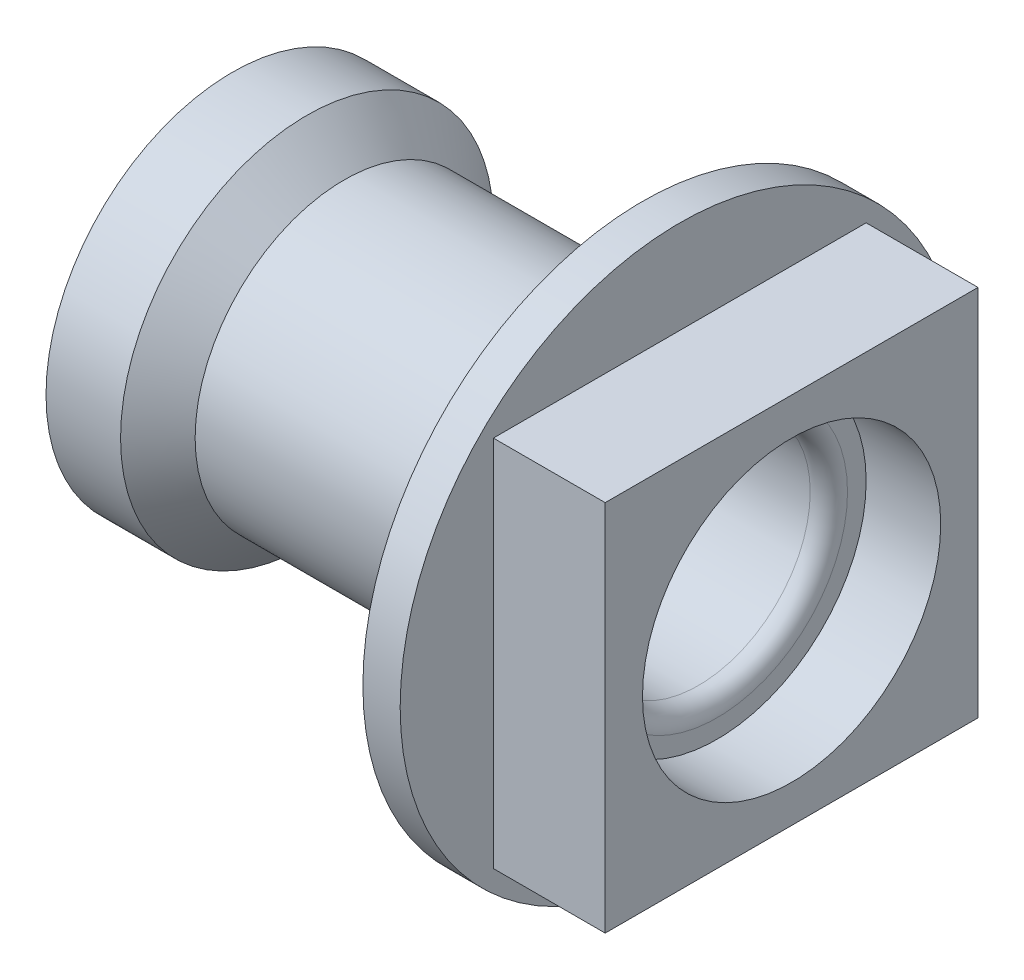
SolidWorks part; units mm, degrees
material "AISI 1045 Aço, trefilado"
ref_plane "Plano frontal" through (0, 0, 0) normal (0, 0, 1) x (1, 0, 0)
ref_plane "Plano superior" through (0, 0, 0) normal (0, 1, 0) x (1, 0, 0)
ref_plane "Plano direito" through (0, 0, 0) normal (1, 0, 0) x (0, 0, -1)
sketch "Esboço1" plane through (0, 0, 0) normal (0, 0, 1) x (1, 0, 0)
  line L0 (0, 0) -> (0, 40) construction
  line L1 (0, 40) -> (10, 30)
  line L2 (10, 30) -> (125, 30)
  line L3 (130, 35) -> (130, 40)
  line L4 (130, 40) -> (150, 40)
  line L5 (150, 40) -> (150, 50)
  line L6 (150, 50) -> (120, 50)
  line L7 (120, 50) -> (120, 75)
  line L8 (120, 75) -> (110, 75)
  line L9 (110, 75) -> (110, 50)
  line L10 (100, 40) -> (30, 40)
  line L11 (30, 40) -> (20, 50)
  line L12 (20, 50) -> (0, 50)
  line L13 (0, 50) -> (0, 40)
  line L14 (0, 0) -> (73.9105, 0) construction
  arc A0 (125, 30) -> (130, 35) centre (125, 35) ccw
  arc A1 (110, 50) -> (100, 40) centre (100, 50) cw
  point P16 (0, 45)
  point P21 (55.2644, 50)
  point P22 (11.2838, 50)
  point P23 (0, 34.3192)
  point P24 (13.2713, 50)
  dimension "D5" = 5
  dimension "D11" = 10
  dimension "D1" = 60
  dimension "D2" = 80
  dimension "D3" = 150
  dimension "D4" = 20
  dimension "D6" = 80
  dimension "D7" = 100
  dimension "D8" = 150
  dimension "D9" = 10
  dimension "D10" = 30
  dimension "D12" = 10
  dimension "D13" = 10
  dimension "D14" = 30
revolve "Revolução1" add sketch "Esboço1" angle 360 about L14
sketch "Esboço2" plane through (150, 0, 0) normal (1, 0, 0) x (0, 0, -1)
  line L1 (-50, -50) -> (50, -50)
  line L2 (-50, -50) -> (-50, 50)
  line L3 (-50, 50) -> (50, 50)
  line L4 (50, -50) -> (50, 50)
  line L5 (-50, -50) -> (50, 50) construction
  line L6 (-50, 50) -> (50, -50) construction
  circle A0 centre (0, 0) radius 50 construction
  circle A1 centre (0, 0) radius 50 construction
  point P0 (0, 0)
  circle M5 centre (0, 0) radius 50
extrude "Ressalto-extrusão1" add sketch "Esboço2" against normal up to surface (30 mm away) contours L3 L2 M5 | L2 L1 M5 | L1 L4 M5 | L4 L3 M5 up to face at (120, 0, 75)
